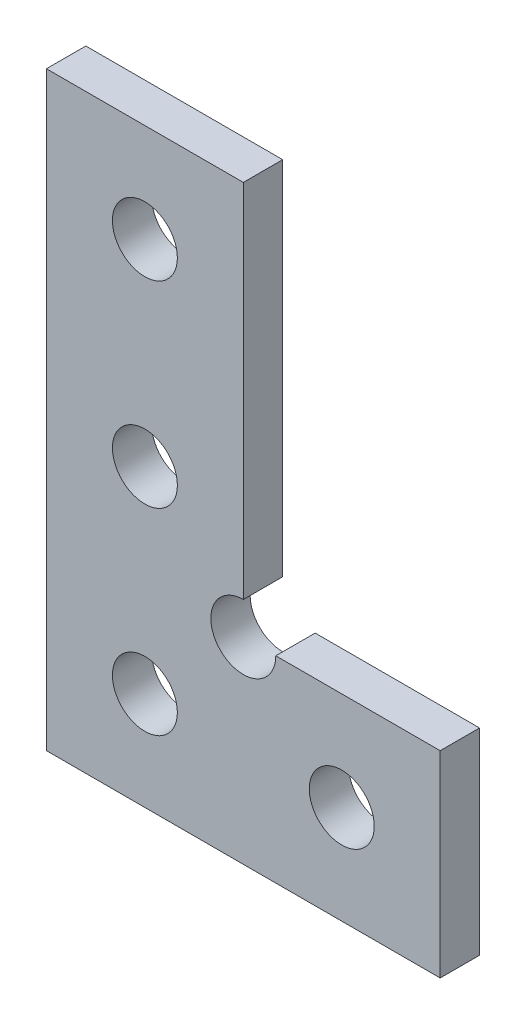
SolidWorks part; units mm, degrees
ref_plane "Front Plane" through (0, 0, 0) normal (0, 0, 1) x (1, 0, 0)
ref_plane "Top Plane" through (0, 0, 0) normal (0, 1, 0) x (1, 0, 0)
ref_plane "Right Plane" through (0, 0, 0) normal (1, 0, 0) x (0, 0, -1)
sketch "Sketch1" plane through (0, 0, 0) normal (0, 0, 1) x (1, 0, 0)
  line L0 (-10, 15) -> (-10, -15)
  line L1 (-10, -15) -> (10, -15)
  line L2 (10, -15) -> (10, -5)
  line L3 (-10, 15) -> (0, 15)
  line L4 (0, 15) -> (0, -3.35)
  line L5 (1.65, -5) -> (10, -5)
  line L6 (-10, -15) -> (10, 15) construction
  line L7 (-5, -10) -> (5, -10) construction
  line L8 (-5, -10) -> (-5, 0) construction
  line L9 (-5, 0) -> (-5, 10) construction
  line L10 (5, -10) -> (10, -10) construction
  line L11 (-5, 10) -> (-5, 15) construction
  circle A0 centre (-5, 10) radius 1.65
  circle A1 centre (-5, 0) radius 1.65
  circle A2 centre (5, -10) radius 1.65
  circle A3 centre (-5, -10) radius 1.65
  arc A4 (0, -3.35) -> (1.65, -5) centre (0, -5) ccw
  dimension "D5" = 10
  dimension "D4" = 3.3
  dimension "D1" = 30
  dimension "D2" = 20
  dimension "D3" = 10
extrude "Boss-Extrude1" add sketch "Sketch1" along normal mid plane 2
